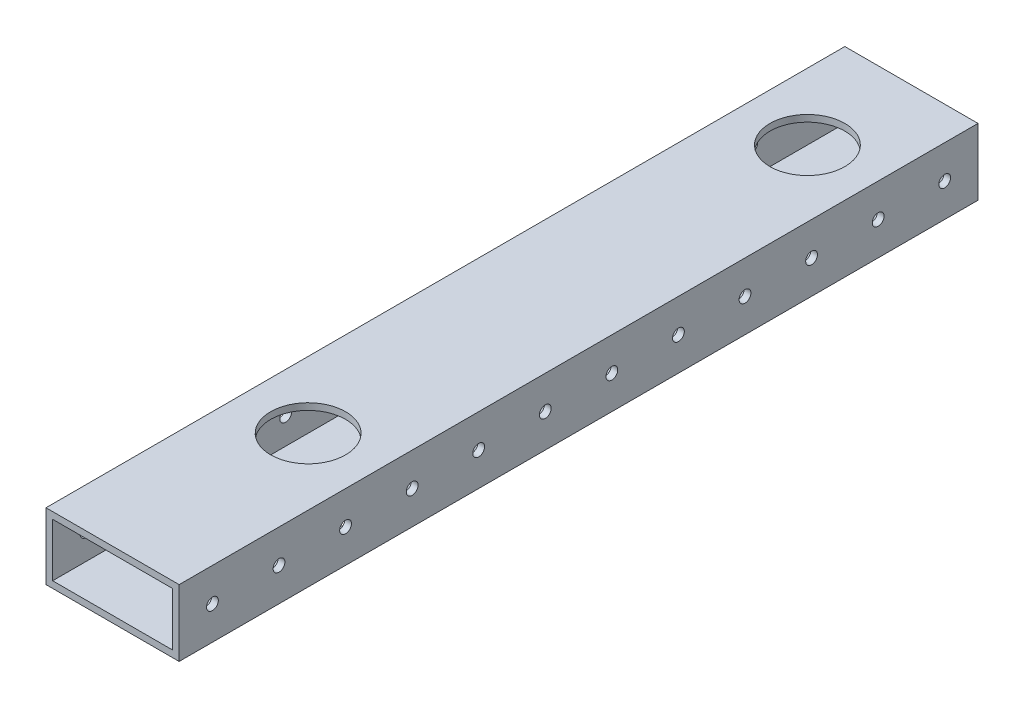
SolidWorks part; units mm, degrees
ref_plane "Front Plane" through (0, 0, 0) normal (0, 0, 1) x (1, 0, 0)
ref_plane "Top Plane" through (0, 0, 0) normal (0, 1, 0) x (1, 0, 0)
ref_plane "Right Plane" through (0, 0, 0) normal (1, 0, 0) x (0, 0, -1)
sketch "Sketch1" plane through (0, 0, 0) normal (0, 0, 1) x (1, 0, 0)
  line L1 (-25.4, -12.7) -> (25.4, -12.7)
  line L2 (-25.4, -12.7) -> (-25.4, 12.7)
  line L3 (-25.4, 12.7) -> (25.4, 12.7)
  line L4 (25.4, -12.7) -> (25.4, 12.7)
  line L5 (-25.4, -12.7) -> (25.4, 12.7) construction
  line L6 (-25.4, 12.7) -> (25.4, -12.7) construction
  line L7 (-22.86, -10.16) -> (22.86, -10.16)
  line L8 (-22.86, -10.16) -> (-22.86, 10.16)
  line L9 (-22.86, 10.16) -> (22.86, 10.16)
  line L10 (22.86, -10.16) -> (22.86, 10.16)
  line L11 (-22.86, -10.16) -> (22.86, 10.16) construction
  line L12 (-22.86, 10.16) -> (22.86, -10.16) construction
  point P0 (0, 0)
  point P6 (0, 0)
  dimension "D1" = 50.8
  dimension "D2" = 25.4
  dimension "D3" = 2.54
  dimension "D4" = 2.54
extrude "Boss-Extrude1" add sketch "Sketch1" against normal blind 533.4
hole_wizard "#8 Clearance Hole1" positions "Sketch2" profile "Sketch3" hole size "#8" standard "ANSI Inch" end condition through all
sketch "Sketch2" plane through (25.4, 0, 0) normal (1, 0, 0) x (0, 0, -1)
  line L0 (533.4, -12.7) -> (0, -12.7) construction
  point P0 (12.7, 0)
  point P16 (38.1, 0)
  point P17 (63.5, 0)
  point P18 (88.9, 0)
  point P19 (114.3, 0)
  point P20 (139.7, 0)
  point P21 (165.1, 0)
  point P22 (190.5, 0)
  point P23 (215.9, 0)
  point P24 (241.3, 0)
  point P25 (266.7, 0)
  point P26 (292.1, 0)
  point P27 (317.5, 0)
  point P28 (342.9, 0)
  point P29 (368.3, 0)
  point P30 (393.7, 0)
  point P31 (419.1, 0)
  point P32 (444.5, 0)
  point P33 (469.9, 0)
  point P34 (495.3, 0)
  point P35 (520.7, 0)
  dimension "D1" = 12.7
  dimension "D2" = 12.7
  dimension "D3" = 21
sketch "Sketch3" plane through (25.4, 0, -12.7) normal (0, 1, 0) x (0, 0, -1)
  line L0 (0, 0) -> (0, 50.8)
  line L1 (0, 50.8) -> (2.2479, 50.8)
  line L2 (2.2479, 50.8) -> (2.2479, 0)
  line L5 (2.2479, 0) -> (0, 0)
  line L11 (0, -6.35) -> (0, 107.95) construction
  dimension "Thru Hole Dia." = 4.4958
  dimension "Thru Hole Depth" = 50.8
sketch "Sketch4" plane through (0, 12.7, 0) normal (0, 1, 0) x (1, 0, 0)
  line L0 (-7.2063, 228.6) -> (135.5131, 228.6)
  line L3 (135.5131, 228.6) -> (135.5131, -17.6414)
  line L4 (135.5131, -17.6414) -> (-94.0569, -17.6414)
  line L5 (-94.0569, -17.6414) -> (-94.0569, 228.6)
  line L6 (-94.0569, 228.6) -> (-7.2063, 228.6)
extrude "Cut-Extrude2" cut sketch "Sketch4" against normal blind 76.962
ref_plane "Plane1" through (-25.4, 12.7, -533.4) normal (0, 0, 1) x (1, 0, 0)
sketch "Sketch5" plane through (0, 12.7, 0) normal (0, 1, 0) x (1, 0, 0)
  circle A0 centre (0, 493.7125) radius 14.2875
  circle A1 centre (0, 303.2125) radius 14.2875
  point P8 (0, 482.6)
  dimension "D2" = 28.575
  dimension "D3" = 190.5
  dimension "D4" = 28.575
extrude "Cut-Extrude3" cut sketch "Sketch5" against normal blind 43.434
